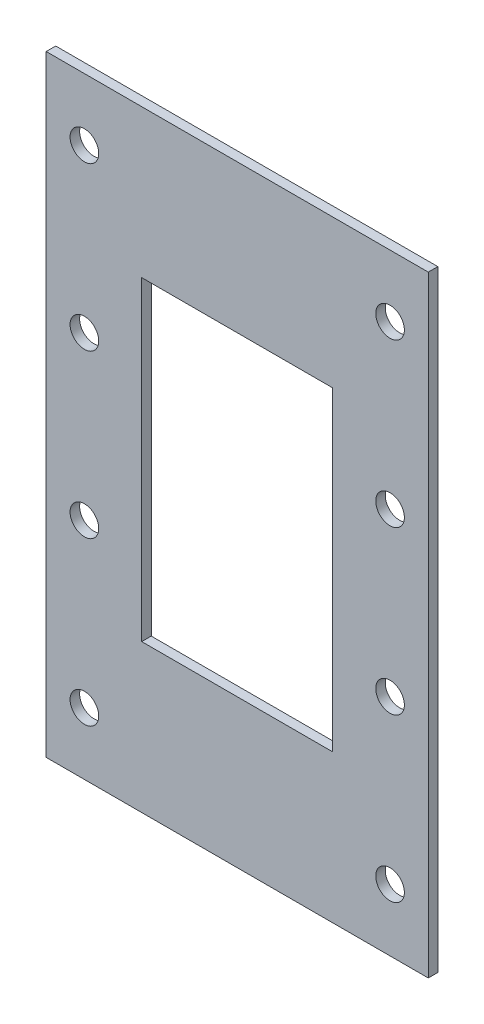
SolidWorks part; units mm, degrees
material "PTFE (general)"
ref_plane "Front Plane" through (0, 0, 0) normal (0, 0, 1) x (1, 0, 0)
ref_plane "Top Plane" through (0, 0, 0) normal (0, 1, 0) x (1, 0, 0)
ref_plane "Right Plane" through (0, 0, 0) normal (1, 0, 0) x (0, 0, -1)
sketch "Sketch1" plane through (0, 0, 0) normal (0, 0, 1) x (1, 0, 0)
  line L1 (0, 37.8259) -> (40, 37.8259)
  line L2 (0, 37.8259) -> (0, -26.1741)
  line L3 (0, -26.1741) -> (40, -26.1741)
  line L4 (40, 37.8259) -> (40, -26.1741)
  dimension "D1" = 64
  dimension "D2" = 40
extrude "Boss-Extrude1" add sketch "Sketch1" along normal blind 1
sketch "Sketch2" plane through (0, 0, 1) normal (0, 0, 1) x (1, 0, 0)
  line L0 (0, 37.8259) -> (0, -26.1741) construction
  line L1 (10, 22.3259) -> (30, 22.3259)
  line L2 (10, 22.3259) -> (10, -10.6741)
  line L3 (10, -10.6741) -> (30, -10.6741)
  line L4 (30, 22.3259) -> (30, -10.6741)
  line L5 (0, -26.1741) -> (40, -26.1741) construction
  line L6 (4, 31.3259) -> (4, -19.6741)
  line L7 (36, 31.3259) -> (36, -19.6741)
  line L8 (40, 37.8259) -> (0, 37.8259) construction
  line L10 (40, -26.1741) -> (40, 37.8259) construction
  circle A0 centre (4, 31.3259) radius 1.5
  circle A1 centre (4, 14.3259) radius 1.5
  circle A2 centre (4, -2.6741) radius 1.5
  circle A3 centre (4, -19.6741) radius 1.5
  circle A4 centre (36, -19.6741) radius 1.5
  circle A5 centre (36, -2.6741) radius 1.5
  circle A6 centre (36, 14.3259) radius 1.5
  circle A7 centre (36, 31.3259) radius 1.5
  point P12 (4, 14.3259)
  point P13 (4, -2.6741)
  point P14 (36, -2.6741)
  point P15 (36, 14.3259)
  dimension "D1" = 20
  dimension "D2" = 10
  dimension "D3" = 33
  dimension "D4" = 15.5
  dimension "D5" = 6.5
  dimension "D6" = 17
  dimension "D7" = 17
  dimension "D8" = 17
  dimension "D9" = 4
  dimension "D10" = 17
  dimension "D11" = 17
  dimension "D12" = 17
  dimension "D13" = 6.5
  dimension "D14" = 4
  dimension "D15" = 32
extrude "Cut-Extrude1" cut sketch "Sketch2" against normal through all both and the other way through all
